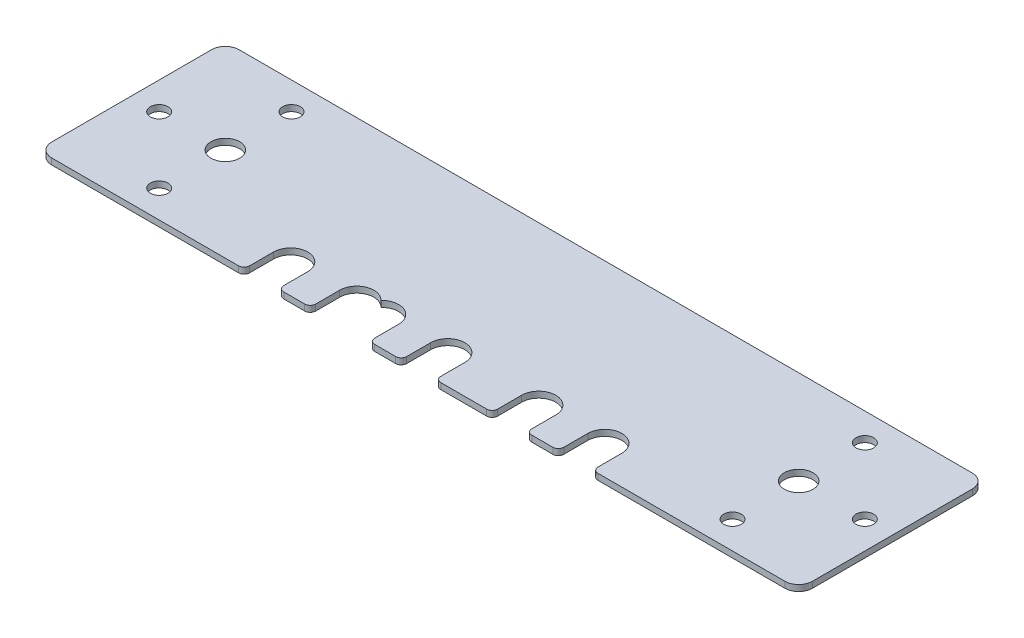
SolidWorks part; units mm, degrees
ref_plane "Front Plane" through (0, 0, 0) normal (0, 0, 1) x (1, 0, 0)
ref_plane "Top Plane" through (0, 0, 0) normal (0, 1, 0) x (1, 0, 0)
ref_plane "Right Plane" through (0, 0, 0) normal (1, 0, 0) x (0, 0, -1)
sketch "Sketch1" plane through (0, 0, 0) normal (0, 1, 0) x (1, 0, 0)
  line L1 (-66.5, -17) -> (66.5, -17)
  line L2 (-69, -14.5) -> (-69, 14.5)
  line L3 (-66.5, 17) -> (66.5, 17)
  line L4 (69, -14.5) -> (69, 14.5)
  line L5 (-69, -17) -> (69, 17) construction
  line L6 (-69, 17) -> (69, -17) construction
  arc A0 (66.5, 17) -> (69, 14.5) centre (66.5, 14.5) cw
  arc A1 (69, -14.5) -> (66.5, -17) centre (66.5, -14.5) cw
  arc A2 (-66.5, -17) -> (-69, -14.5) centre (-66.5, -14.5) cw
  arc A3 (-66.5, 17) -> (-69, 14.5) centre (-66.5, 14.5) ccw
  point P1 (0, 0)
  dimension "D3" = 2.5
  dimension "D1" = 138
  dimension "D2" = 34
extrude "Boss-Extrude1" add sketch "Sketch1" along normal blind 1.11
sketch "Sketch3" plane through (0, -10, 0) normal (0, 1, 0) x (1, 0, 0)
  line L4 (-52, 12) -> (-52, -12) construction
  line L5 (-52, 0) -> (-64, 0) construction
  line L6 (52, 12) -> (52, -12) construction
  line L7 (52, 0) -> (64, 0) construction
  line L8 (-69, 14.5) -> (-69, -14.5) construction
  line L9 (69, -14.5) -> (69, 14.5) construction
  circle A0 centre (-52, 0) radius 2.6
  circle A1 centre (52, 0) radius 2.6
  circle A4 centre (-52, 12) radius 1.6
  circle A5 centre (-52, -12) radius 1.6
  circle A6 centre (52, -12) radius 1.6
  circle A7 centre (52, 12) radius 1.6
  circle A14 centre (-64, 0) radius 1.6
  circle A15 centre (64, 0) radius 1.6
  dimension "D2" = 12
  dimension "D3" = 3.2
  dimension "D4" = 3.2
  dimension "D5" = 3.2
  dimension "D9" = 3.2
  dimension "D10" = 3.2
  dimension "D11" = 3.2
  dimension "D13" = 12
  dimension "D15" = 5.2
  dimension "D16" = 5.2
  dimension "D1" = 12
  dimension "D6" = 12
  dimension "D7" = 12
  dimension "D8" = 17
  dimension "D12" = 12
  dimension "D14" = 17
extrude "Cut-Extrude5" cut sketch "Sketch3" along normal through all
sketch "Sketch4" plane through (0, 0, 0) normal (0, -1, 0) x (1, 0, 0)
  circle A0 centre (0, 11.655) radius 3.1
  circle A1 centre (-12, 11.655) radius 3.1
  dimension "D1" = 6.2
  dimension "D2" = 6.2
extrude "Cut-Extrude6" cut sketch "Sketch4" against normal through all
sketch "Sketch5" plane through (0, 0, 0) normal (0, -1, 0) x (1, 0, 0)
  circle A0 centre (-16.5, 11.655) radius 3.1
  circle A1 centre (-28.5, 11.655) radius 3.1
  circle A2 centre (28.5, 11.655) radius 3.1
  circle A3 centre (16.5, 11.655) radius 3.1
  dimension "D1" = 6.2
  dimension "D2" = 6.2
  dimension "D3" = 6.2
  dimension "D4" = 6.2
extrude "Cut-Extrude7" cut sketch "Sketch5" against normal through all
sketch "Sketch6" plane through (0, 1.11, 0) normal (0, 1, 0) x (1, 0, 0)
  line L0 (-31.6, -11.655) -> (-25.4, -11.655)
  line L1 (-31.6, -11.655) -> (-31.6, -17.655)
  line L2 (-25.4, -11.655) -> (-25.4, -17.655)
  line L3 (-31.6, -17.655) -> (-25.4, -17.655)
  line L4 (-19.6, -11.655) -> (-8.9, -11.655)
  line L5 (-19.6, -11.655) -> (-19.6, -17.655)
  line L6 (-8.9, -11.655) -> (-8.9, -17.655)
  line L7 (-19.6, -17.655) -> (-8.9, -17.655)
  line L9 (-3.1, -11.655) -> (3.1, -11.655)
  line L10 (-3.1, -11.655) -> (-3.1, -17.655)
  line L11 (3.1, -11.655) -> (3.1, -17.655)
  line L12 (-3.1, -17.655) -> (3.1, -17.655)
  line L13 (25.4, -11.655) -> (31.6, -11.655)
  line L14 (25.4, -11.655) -> (25.4, -17.655)
  line L15 (31.6, -11.655) -> (31.6, -17.655)
  line L16 (25.4, -17.655) -> (31.6, -17.655)
  line L17 (13.4, -11.655) -> (19.6, -11.655)
  line L18 (13.4, -11.655) -> (13.4, -17.655)
  line L19 (19.6, -11.655) -> (19.6, -17.655)
  line L20 (13.4, -17.655) -> (19.6, -17.655)
  circle A0 centre (-28.5, -11.655) radius 3.1 construction
  arc A1 (-14.25, -9.5225) -> (-14.25, -13.7875) centre (-16.5, -11.655) ccw construction
  arc A2 (-14.25, -13.7875) -> (-14.25, -9.5225) centre (-12, -11.655) ccw construction
  circle A3 centre (0, -11.655) radius 3.1 construction
  circle A4 centre (28.5, -11.655) radius 3.1 construction
  circle A5 centre (16.5, -11.655) radius 3.1 construction
  dimension "D1" = 6
  dimension "D2" = 6
  dimension "D3" = 6
  dimension "D4" = 6
  dimension "D5" = 6
extrude "Cut-Extrude8" cut sketch "Sketch6" against normal through all
fillet "Fillet1" radius 1 10 edges at (19.6, 0.555, 17) (31.6, 0.555, 17) (13.4, 0.555, 17) (25.4, 0.555, 17) (3.1, 0.555, 17) (-3.1, 0.555, 17) (-8.9, 0.555, 17) (-25.4, 0.555, 17) (-19.6, 0.555, 17) (-31.6, 0.555, 17)
